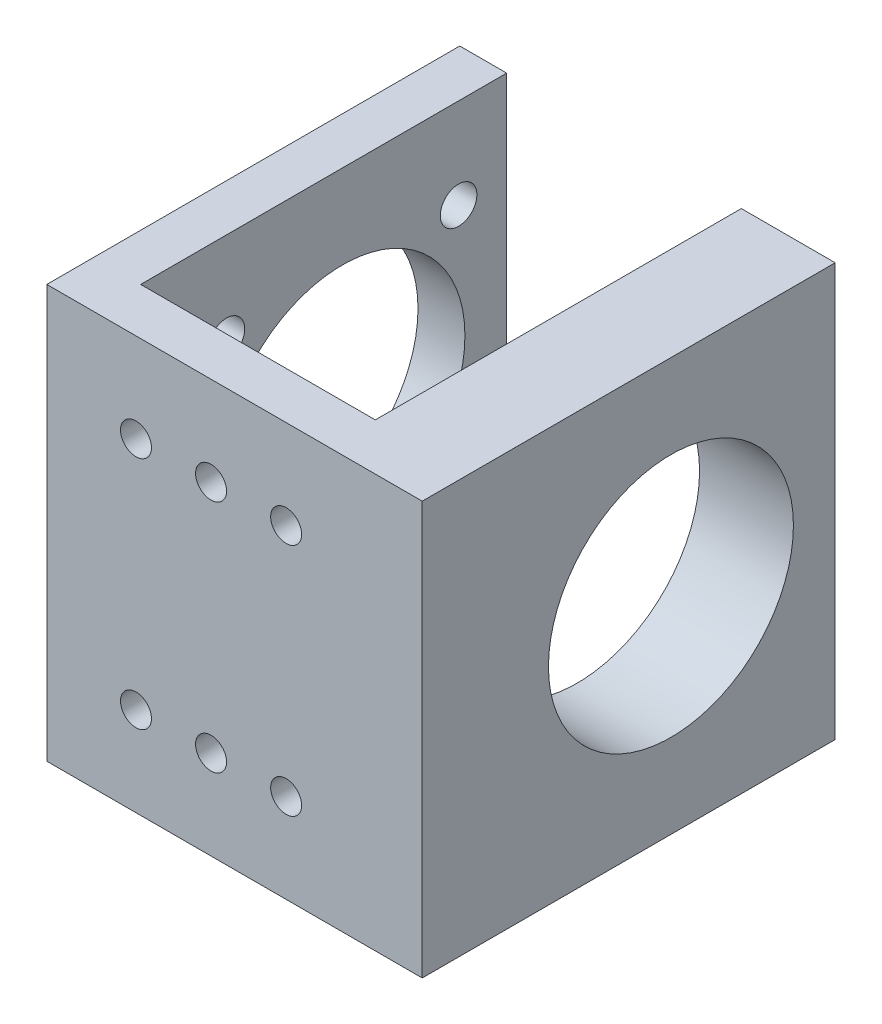
SolidWorks part; units mm, degrees
ref_plane "前视基准面" through (0, 0, 0) normal (0, 0, 1) x (1, 0, 0)
ref_plane "上视基准面" through (0, 0, 0) normal (0, 1, 0) x (1, 0, 0)
ref_plane "右视基准面" through (0, 0, 0) normal (1, 0, 0) x (0, 0, -1)
sketch "草图1" plane through (0, 0, 0) normal (0, 1, 0) x (1, 0, 0)
  line L0 (-47.2331, -18.4776) -> (-47.2331, -62.4776)
  line L1 (-47.2331, -62.4776) -> (-7.2331, -62.4776)
  line L2 (-7.2331, -62.4776) -> (-7.2331, -18.4776)
  line L3 (-7.2331, -18.4776) -> (-17.2331, -18.4776)
  line L4 (-17.2331, -18.4776) -> (-17.2331, -57.4776)
  line L5 (-17.2331, -57.4776) -> (-42.2331, -57.4776)
  line L6 (-42.2331, -57.4776) -> (-42.2331, -18.4776)
  line L7 (-42.2331, -18.4776) -> (-47.2331, -18.4776)
extrude "凸台-拉伸1" add sketch "草图1" along normal blind 44
sketch "草图3" plane through (0, 0, 57.4776) normal (0, 0, -1) x (-1, 0, 0)
  circle A0 centre (37.7331, 34.5) radius 1.65
  circle A1 centre (37.7331, 9.5) radius 1.65
  circle A2 centre (29.7331, 34.5) radius 1.65
  circle A3 centre (29.7331, 9.5) radius 1.65
  circle A4 centre (21.7331, 34.5) radius 1.65
  circle A5 centre (21.7331, 9.5) radius 1.65
  dimension "D1" = 2
  dimension "D2" = 3
extrude "切除-拉伸1" cut sketch "草图3" against normal blind 44
sketch "草图4" plane through (-7.2331, 0, 0) normal (1, 0, 0) x (0, 0, -1)
  circle A0 centre (-23.6032, 9.625) radius 1.95
  circle A1 centre (-48.3432, 9.625) radius 1.95
  circle A2 centre (-23.6032, 34.375) radius 1.95
  circle A3 centre (-48.3432, 34.375) radius 1.95
  circle A4 centre (-35.9776, 22) radius 13.05
  dimension "D1" = 2
  dimension "D2" = 2
sketch "草图6" plane through (-47.2331, 0, 0) normal (-1, 0, 0) x (0, 0, 1)
  circle A3 centre (48.3432, 34.375) radius 1.95
  circle A4 centre (48.3432, 34.375) radius 1.95
  circle A5 centre (23.6032, 34.375) radius 1.95
  circle A6 centre (23.6032, 34.375) radius 1.95
  circle A7 centre (48.3432, 9.625) radius 1.95
  circle A8 centre (48.3432, 9.625) radius 1.95
  circle A9 centre (23.6032, 9.625) radius 1.95
  circle A10 centre (23.6032, 9.625) radius 1.95
  dimension "D2" = 0
  dimension "D3" = 0
  dimension "D4" = 0
  dimension "D5" = 0
extrude "切除-拉伸5" cut sketch "草图6" against normal up to surface (5 mm away) up to face at (-42.2331, 22, 37.9776)
extrude "切除-拉伸6" cut sketch "草图4" against normal blind 53 contours A4
